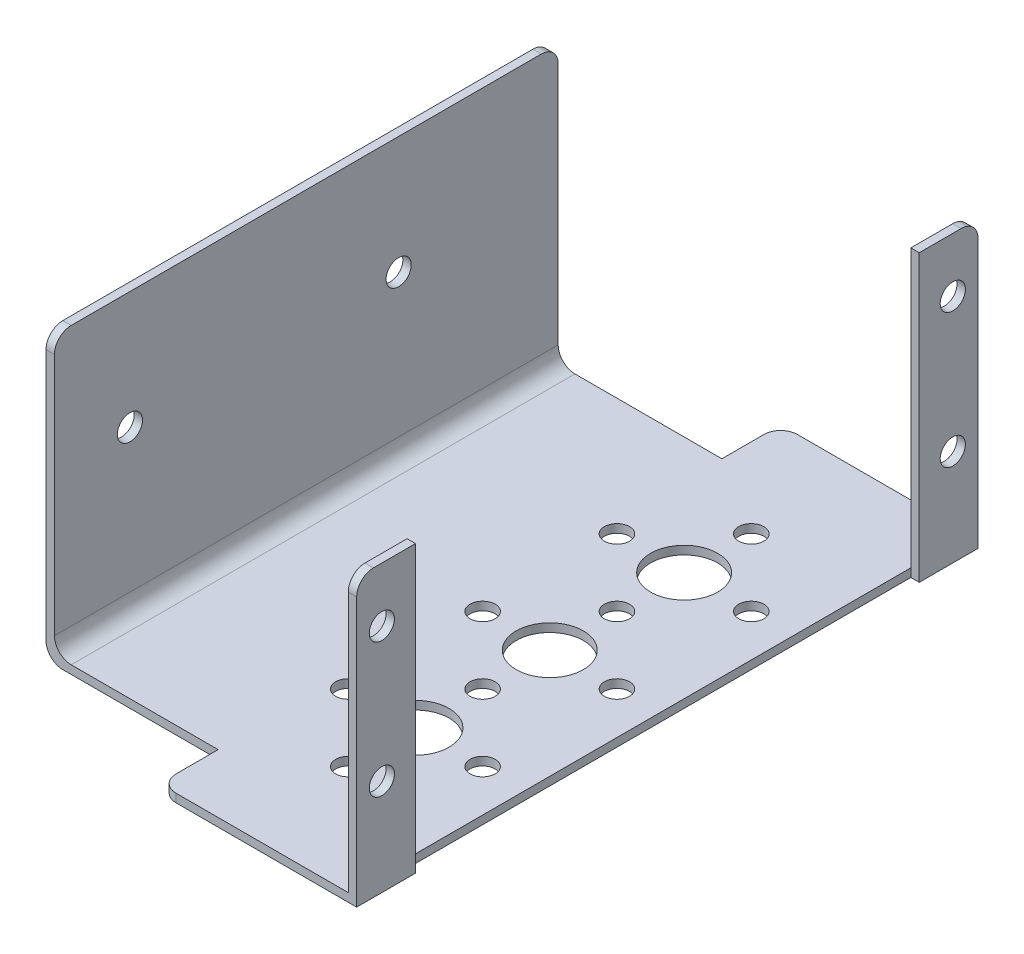
SolidWorks part; units mm, degrees
material "Plain Carbon Steel"
ref_plane "Front Plane" through (0, 0, 0) normal (0, 0, 1) x (1, 0, 0)
ref_plane "Top Plane" through (0, 0, 0) normal (0, 1, 0) x (1, 0, 0)
ref_plane "Right Plane" through (0, 0, 0) normal (1, 0, 0) x (0, 0, -1)
sketch "Sketch1" plane through (0, 0, 0) normal (0, 0, 1) x (1, 0, 0)
  line L0 (-68.2124, 4.5861) -> (-68.2124, -28.4139)
  line L1 (-68.2124, -28.4139) -> (-26.2124, -28.4139)
  line L2 (-26.2124, -28.4139) -> (-26.2124, 4.5861)
  line L3 (-69.2124, 4.5861) -> (-69.2124, -29.4139)
  line L4 (-69.2124, -29.4139) -> (-25.2124, -29.4139)
  line L5 (-25.2124, -29.4139) -> (-25.2124, 4.5861)
  line L6 (-69.2124, 4.5861) -> (-68.2124, 4.5861)
  line L7 (-25.2124, 4.5861) -> (-26.2124, 4.5861)
  dimension "D1" = 1
extrude "Boss-Extrude1" add sketch "Sketch1" along normal blind 74
sketch "Sketch2" plane through (-25.2124, 0, 0) normal (1, 0, 0) x (0, 0, -1)
  line L0 (-74, 4.5861) -> (0, 4.5861) construction
  line L1 (0, -29.4139) -> (0, 4.5861) construction
  line L2 (-74, -29.4139) -> (-74, 4.5861) construction
  circle A0 centre (-3, -1.9139) radius 1.5
  circle A1 centre (-71, -1.9139) radius 1.5
  circle A2 centre (-71, -17.9139) radius 1.5
  circle A3 centre (-3, -17.9139) radius 1.5
  dimension "D1" = 2
  dimension "D3" = 6.5
  dimension "D4" = 3
  dimension "D2" = 2
extrude "Cut-Extrude1" cut sketch "Sketch2" against normal blind 1
sketch "Sketch4" plane through (-25.2124, 0, 0) normal (1, 0, 0) x (0, 0, -1)
  line L0 (-74, 4.5861) -> (0, 4.5861) construction
  line L1 (-7, 4.5861) -> (-67, 4.5861)
  line L2 (-7, 4.5861) -> (-7, -29.4139)
  line L3 (-7, -29.4139) -> (-67, -29.4139)
  line L4 (-67, 4.5861) -> (-67, -29.4139)
  line L5 (-74, -29.4139) -> (0, -29.4139) construction
  line L6 (-74, -29.4139) -> (-74, 4.5861) construction
  line L8 (0, -29.4139) -> (0, 4.5861) construction
  dimension "D1" = 7
  dimension "D3" = 60
extrude "Cut-Extrude2" cut sketch "Sketch4" against normal blind 1
sketch "Sketch6" plane through (-69.2124, 0, 0) normal (-1, 0, 0) x (0, 0, 1)
  line L0 (74, -29.4139) -> (0, -29.4139) construction
  line L1 (0, 4.5861) -> (7, 4.5861)
  line L2 (0, 4.5861) -> (0, -29.4139)
  line L3 (0, -29.4139) -> (7, -29.4139)
  line L4 (7, 4.5861) -> (7, -29.4139)
  line L5 (74, 4.5861) -> (0, 4.5861) construction
  line L6 (74, -29.4139) -> (67, -29.4139)
  line L7 (74, -29.4139) -> (74, 4.5861)
  line L8 (74, 4.5861) -> (67, 4.5861)
  line L9 (67, -29.4139) -> (67, 4.5861)
extrude "Cut-Extrude3" cut sketch "Sketch6" against normal blind 1
sketch "Sketch7" plane through (-69.2124, 0, 0) normal (-1, 0, 0) x (0, 0, 1)
  line L0 (67, 4.5861) -> (67, -29.4139) construction
  line L1 (67, 4.5861) -> (7, 4.5861) construction
  circle A0 centre (58, -9.4139) radius 1.5
  circle A1 centre (26, -9.4139) radius 1.5
  point P2 (67, -12.4139)
  dimension "D1" = 9
  dimension "D3" = 3
  dimension "D2" = 14
  dimension "D4" = 2
extrude "Cut-Extrude4" cut sketch "Sketch7" against normal blind 1
sketch "Sketch8" plane through (0, -29.4139, 0) normal (0, -1, 0) x (-1, 0, 0)
  line L0 (68.2124, -74) -> (25.2124, -74) construction
  line L1 (25.2124, -7) -> (25.2124, 0) construction
  circle A0 centre (39.2124, -37) radius 4
  circle A1 centre (39.2124, -29) radius 1.5
  circle A2 centre (47.2124, -37) radius 1.5
  circle A3 centre (39.2124, -45) radius 1.5
  circle A4 centre (31.2124, -37) radius 1.5
  circle A5 centre (31.2124, -21) radius 1.5
  circle A6 centre (39.2124, -13) radius 1.5
  circle A7 centre (47.2124, -21) radius 1.5
  circle A8 centre (39.2124, -21) radius 4
  circle A9 centre (39.2124, -29) radius 1.5
  circle A10 centre (39.2124, -61) radius 1.5
  circle A11 centre (39.2124, -53) radius 4
  circle A12 centre (47.2124, -53) radius 1.5
  circle A13 centre (31.2124, -53) radius 1.5
  circle A14 centre (39.2124, -45) radius 1.5
  point P17 (39.2124, -37)
  dimension "D1" = 37
  dimension "D2" = 14
  dimension "D3" = 4
  dimension "D4" = 2
  dimension "D5" = 2
extrude "Cut-Extrude5" cut sketch "Sketch8" against normal blind 1 contours A13 | A10 | A12 | A11 | A3 | A2 | A0 | A4 | A1 | A8 | A5 | A6 | A7
sketch "Sketch9" plane through (0, -29.4139, 0) normal (0, -1, 0) x (1, 0, 0)
  line L1 (-68.2124, 0) -> (-48.7124, 0)
  line L2 (-68.2124, 0) -> (-68.2124, 7)
  line L3 (-68.2124, 7) -> (-48.7124, 7)
  line L4 (-48.7124, 0) -> (-48.7124, 7)
  line L5 (-68.2124, 74) -> (-48.7124, 74)
  line L6 (-68.2124, 74) -> (-68.2124, 67)
  line L7 (-68.2124, 67) -> (-48.7124, 67)
  line L8 (-48.7124, 74) -> (-48.7124, 67)
extrude "Cut-Extrude6" cut sketch "Sketch9" against normal blind 1
fillet "Fillet1" radius 2 8 edges at (-25.7124, 4.5861, 74) (-25.7124, 4.5861, 0) (-68.2124, -28.4139, 37) (-48.7124, -28.9139, 0) (-48.7124, -28.9139, 74) (-68.7124, 4.5861, 7) (-68.7124, 4.5861, 67) (-69.2124, -29.4139, 37)
